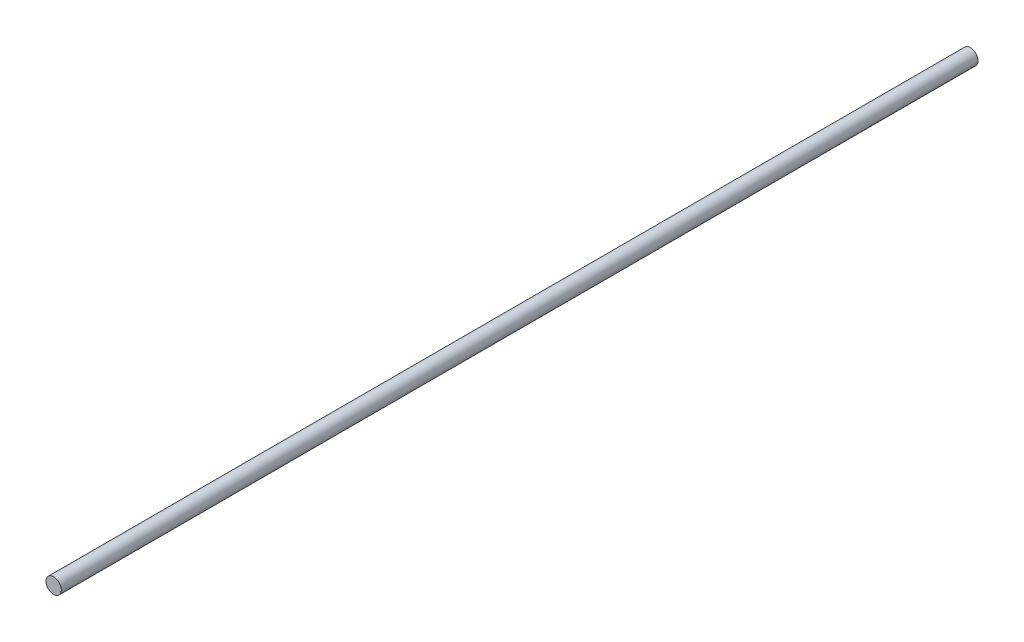
SolidWorks part; units mm, degrees
ref_plane "Plan de face" through (0, 0, 0) normal (0, 0, 1) x (1, 0, 0)
ref_plane "Plan de dessus" through (0, 0, 0) normal (0, 1, 0) x (1, 0, 0)
ref_plane "Plan de droite" through (0, 0, 0) normal (1, 0, 0) x (0, 0, -1)
sketch "Esquisse1" plane through (0, 0, 0) normal (0, 0, 1) x (1, 0, 0)
  circle A0 centre (0, 0) radius 2.5
  dimension "D1" = 5
extrude "Boss.-Extru.1" add sketch "Esquisse1" along normal blind 298.65
